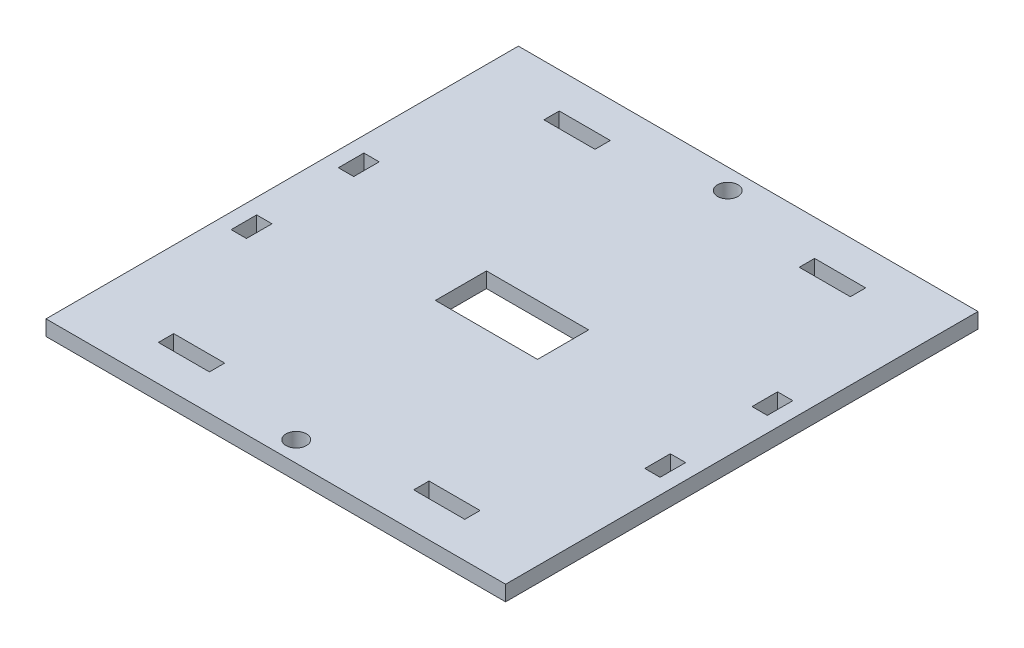
SolidWorks part; units mm, degrees
ref_plane "Front Plane" through (0, 0, 0) normal (0, 0, 1) x (1, 0, 0)
ref_plane "Top Plane" through (0, 0, 0) normal (0, 1, 0) x (1, 0, 0)
ref_plane "Right Plane" through (0, 0, 0) normal (1, 0, 0) x (0, 0, -1)
sketch "Sketch2" plane through (0, 0, 0) normal (0, 1, 0) x (1, 0, 0)
  line L0 (-45, -46.25) -> (45, -46.25)
  line L1 (-45, -46.25) -> (-45, 46.25)
  line L2 (-45, 46.25) -> (45, 46.25)
  line L3 (45, -46.25) -> (45, 46.25)
  line L16 (-20, 39.25) -> (-30, 39.25)
  line L17 (-20, 36.25) -> (-20, 39.25)
  line L18 (-30, 36.25) -> (-20, 36.25)
  line L19 (-30, 39.25) -> (-30, 36.25)
  line L28 (-42, 13) -> (-39, 13)
  line L29 (-42, 8) -> (-42, 13)
  line L30 (-39, 8) -> (-42, 8)
  line L31 (-39, 13) -> (-39, 8)
  line L36 (0, 46.25) -> (0, -46.25) construction
  line L37 (-45, 0) -> (45, 0) construction
  line L38 (20, 36.25) -> (20, 39.25)
  line L39 (30, 36.25) -> (20, 36.25)
  line L40 (30, 39.25) -> (30, 36.25)
  line L41 (20, 39.25) -> (30, 39.25)
  line L42 (30, -36.25) -> (20, -36.25)
  line L43 (30, -39.25) -> (30, -36.25)
  line L44 (20, -39.25) -> (30, -39.25)
  line L45 (20, -36.25) -> (20, -39.25)
  line L46 (-20, -36.25) -> (-20, -39.25)
  line L47 (-30, -36.25) -> (-20, -36.25)
  line L48 (-30, -39.25) -> (-30, -36.25)
  line L49 (-20, -39.25) -> (-30, -39.25)
  line L50 (-42, -8) -> (-42, -13)
  line L51 (-39, -8) -> (-42, -8)
  line L52 (-39, -13) -> (-39, -8)
  line L53 (-42, -13) -> (-39, -13)
  line L54 (42, 8) -> (42, 13)
  line L55 (39, 8) -> (42, 8)
  line L56 (39, 13) -> (39, 8)
  line L57 (42, 13) -> (39, 13)
  line L58 (39, -8) -> (42, -8)
  line L59 (39, -13) -> (39, -8)
  line L60 (42, -13) -> (39, -13)
  line L61 (42, -8) -> (42, -13)
  line L63 (-10, -5) -> (10, -5)
  line L64 (-10, -5) -> (-10, 5)
  line L65 (-10, 5) -> (10, 5)
  line L66 (10, -5) -> (10, 5)
  line L67 (-10, -5) -> (10, 5) construction
  line L68 (-10, 5) -> (10, -5) construction
  circle A0 centre (0, -42.25) radius 2
  circle A1 centre (0, 42.25) radius 2
  point P40 (0, 0)
  dimension "D10" = 4
  dimension "D11" = 4
  dimension "D1" = 92.5
  dimension "D2" = 90
  dimension "D3" = 3
  dimension "D4" = 3
  dimension "D5" = 10
  dimension "D6" = 3
  dimension "D7" = 5
  dimension "D8" = 20
  dimension "D9" = 10
  dimension "D12" = 8
  dimension "D13" = 8
  dimension "D18" = 7
  dimension "D20" = 15
extrude "Boss-Extrude1" add sketch "Sketch2" along normal blind 3
